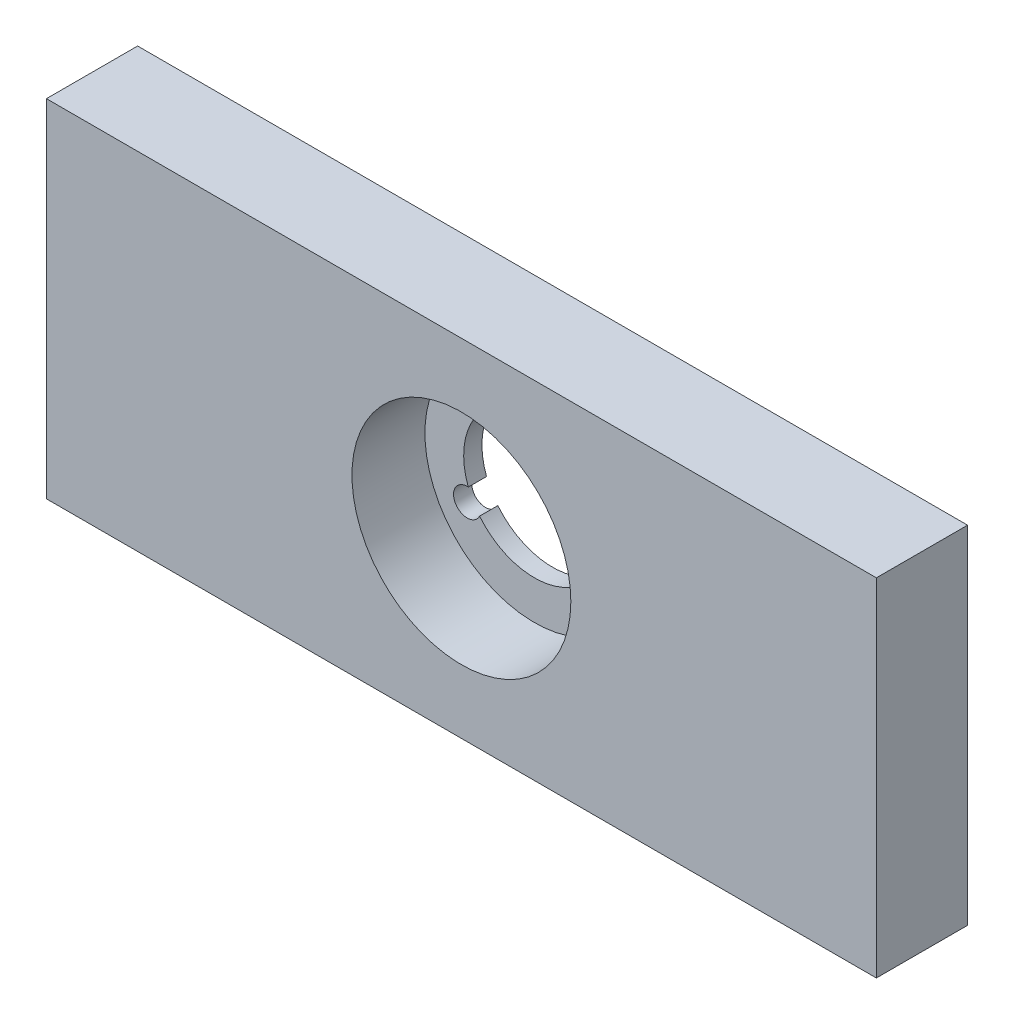
SolidWorks part; units mm, degrees
ref_plane "Plan de face" through (0, 0, 0) normal (0, 0, 1) x (1, 0, 0)
ref_plane "Plan de dessus" through (0, 0, 0) normal (0, 1, 0) x (1, 0, 0)
ref_plane "Plan de droite" through (0, 0, 0) normal (1, 0, 0) x (0, 0, -1)
sketch "Esquisse1" plane through (0, 0, 0) normal (0, 0, 1) x (1, 0, 0)
  line L0 (0, 0) -> (91, 0)
  line L1 (91, 0) -> (91, -38)
  line L2 (91, -38) -> (0, -38)
  line L3 (0, -38) -> (0, 0)
  line L5 (45.5, -19) -> (45.5, 0) construction
  line L6 (45.5, -19) -> (0, -19) construction
  arc A0 (44.2636, -11.3493) -> (38.2561, -21.7546) centre (45.5, -19) ccw
  arc A1 (46.7364, -11.3493) -> (44.2636, -11.3493) centre (45.5, -10.5) ccw
  arc A2 (51.5075, -23.8961) -> (52.7439, -21.7546) centre (52.8612, -23.25) ccw
  arc A3 (38.2561, -21.7546) -> (39.4925, -23.8961) centre (38.1388, -23.25) ccw
  arc A4 (52.7439, -21.7546) -> (46.7364, -11.3493) centre (45.5, -19) ccw
  arc A5 (39.4925, -23.8961) -> (51.5075, -23.8961) centre (45.5, -19) ccw
  dimension "D1" = 38
  dimension "D5" = 7.75
  dimension "D6" = 1.5
  dimension "D2" = 91
  dimension "D7" = 8.5
  dimension "D8" = 8.5
  dimension "D9" = 8.5
extrude "Extrusion1" add sketch "Esquisse1" along normal blind 10
sketch "Esquisse3" plane through (0, 0, 10) normal (0, 0, 1) x (1, 0, 0)
  circle A0 centre (45.5, -19) radius 12
  dimension "D1" = 24
extrude "Extrusion3" cut sketch "Esquisse3" against normal blind 8
